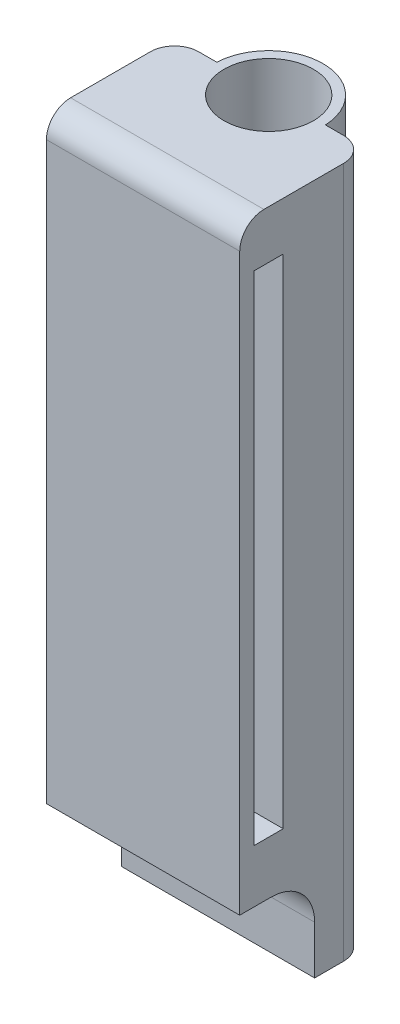
SolidWorks part; units mm, degrees
ref_plane "Front Plane" through (0, 0, 0) normal (0, 0, 1) x (1, 0, 0)
ref_plane "Top Plane" through (0, 0, 0) normal (0, 1, 0) x (1, 0, 0)
ref_plane "Right Plane" through (0, 0, 0) normal (1, 0, 0) x (0, 0, -1)
sketch "Sketch1" plane through (0, 0, 0) normal (0, 1, 0) x (1, 0, 0)
  line L0 (0, -26) -> (-20, -26)
  line L1 (0, -26) -> (20, -26)
  line L2 (-20, -26) -> (-20, -4.5)
  line L3 (-20, -4.5) -> (-20, -2.5)
  line L4 (-17, 0.5) -> (-11.2389, 0.5)
  line L5 (0, -26) -> (0, -20.3135) construction
  line L6 (17, 0.5) -> (11.2389, 0.5)
  line L7 (20, -4.5) -> (20, -2.5)
  line L8 (20, -26) -> (20, -4.5)
  line L9 (20, -2.5) -> (20, 0.5)
  line L10 (20, 0.5) -> (17, 0.5)
  line L11 (-17, 0.5) -> (-20, 0.5)
  line L12 (-20, 0.5) -> (-20, -2.5)
  circle A0 centre (0, 0) radius 9.25
  arc A1 (11.2389, 0.5) -> (-11.2389, 0.5) centre (0, 0) ccw
  point P12 (-20, 0.5)
  dimension "D1" = 18.5
  dimension "D4" = 2
  dimension "D2" = 26
  dimension "D3" = 20
  dimension "D5" = 21.5
  dimension "D6" = 5
extrude "Boss-Extrude1" add sketch "Sketch1" along normal blind 143
fillet "Fillet2" radius 5 2 edges at (-20, 71.5, -0.5) (20, 71.5, -0.5)
sketch "Sketch2" plane through (20, 0, 0) normal (1, 0, 0) x (0, 0, -1)
  line L0 (-26, 143) -> (-26, 0) construction
  line L1 (-23, 133) -> (-17, 133)
  line L2 (-23, 133) -> (-23, 30)
  line L3 (-23, 30) -> (-17, 30)
  line L4 (-17, 133) -> (-17, 30)
  line L5 (-26, 143) -> (-4.5, 143) construction
  line L6 (-26, 0) -> (-4.5, 0) construction
  dimension "D1" = 6
  dimension "D2" = 3
  dimension "D3" = 10
  dimension "D4" = 30
extrude "Cut-Extrude1" cut sketch "Sketch2" against normal offset from surface (37 mm away) 3 up to face at (-20, 71.5, 15.25)
fillet "Fillet3" radius 5 2 edges at (0, 0, 26) (0, 143, 26)
sketch "Sketch3" plane through (20, 0, 0) normal (1, 0, 0) x (0, 0, -1)
  line L0 (-10.5, 0) -> (-10.5, 10)
  line L1 (-21, 0) -> (-4.5, 0) construction
  line L2 (-19.5, 19) -> (-26, 19)
  line L3 (-26, 138) -> (-26, 5) construction
  line L4 (-26, 19) -> (-26, 5)
  line L5 (-21, 0) -> (-10.5, 0)
  arc A0 (-10.5, 10) -> (-19.5, 19) centre (-19.5, 10) ccw
  arc A1 (-26, 5) -> (-21, 0) centre (-21, 5) ccw
  dimension "D1" = 19
  dimension "D2" = 15.5
  dimension "D3" = 10
extrude "Cut-Extrude2" cut sketch "Sketch3" against normal blind 53
